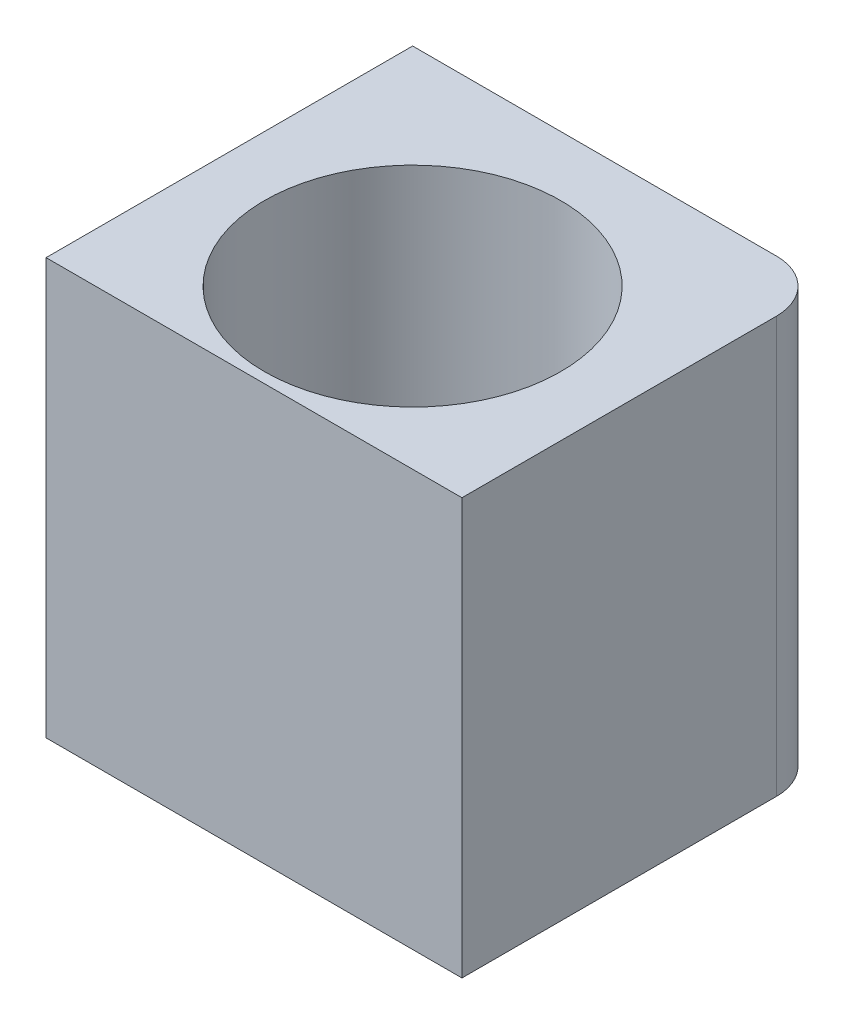
SolidWorks part; units mm, degrees
ref_plane "Alzado" through (0, 0, 0) normal (0, 0, 1) x (1, 0, 0)
ref_plane "Planta" through (0, 0, 0) normal (0, 1, 0) x (1, 0, 0)
ref_plane "Vista lateral" through (0, 0, 0) normal (1, 0, 0) x (0, 0, -1)
sketch "Croquis1" plane through (0, 0, 0) normal (0, 1, 0) x (1, 0, 0)
  line L0 (0, 20) -> (0, -20) construction
  line L1 (-20, 20) -> (20, 20)
  line L2 (-20, 20) -> (-20, -20)
  line L3 (-20, -20) -> (20, -20)
  line L4 (20, 20) -> (20, -20)
  line L5 (-20, 20) -> (20, -20) construction
  line L6 (-20, -20) -> (20, 20) construction
  line L7 (-20, -4.25) -> (-30, -7.25)
  line L8 (-30, -7.25) -> (-30, -15.25)
  line L9 (-30, -15.25) -> (30, -15.25)
  line L10 (20, -4.25) -> (30, -7.25)
  line L11 (30, -7.25) -> (30, -15.25)
  circle A0 centre (-15, 15) radius 2.125
  circle A1 centre (15, 15) radius 2.125
  circle A4 centre (0, 0) radius 15.25
  circle A5 centre (-15, -15) radius 2.125 [skipped]
  circle A6 centre (15, -15) radius 2.125 [skipped]
  point P0 (0, 0)
  point P25 (0, -15.25)
  dimension "D3" = 4.25
  dimension "D7" = 30.5
  dimension "D1" = 40
  dimension "D2" = 40
  dimension "D4" = 5
  dimension "D5" = 2
  dimension "D8" = 8
  dimension "D9" = 10
  dimension "D10" = 15.25
  dimension "D12" = 3
  dimension "D6" = 2
extrude "Soporte caja reductora" add sketch "Croquis1" against normal blind 20
sketch "Croquis3" plane through (0, 0, 15.25) normal (0, 0, 1) x (1, 0, 0)
  line L3 (-20, -20) -> (-20, 0) construction
  circle A0 centre (-23.5, -10) radius 2.125
  circle A1 centre (23.5, -10) radius 2.125
  dimension "D1" = 4.25
  dimension "D2" = 3.5
extrude "Cortar-Extruir1" cut sketch "Croquis3" against normal through all
fillet "Redondeo1" radius 5 2 edges at (-20, -10, -20) (20, -10, -20)
sketch "Sketch1" plane through (0, 0, 0) normal (0, 1, 0) x (1, 0, 0)
  line L0 (15, 20) -> (30, 20)
  line L1 (30, 20) -> (30, 8)
  line L2 (30, 8) -> (25.5, 8)
  line L4 (25.5, 8) -> (25.5, 15)
  line L5 (25.5, 15) -> (20, 15)
  circle A0 centre (15, 15) radius 5
  arc M37 (20, 15) -> (15, 20) centre (15, 15) ccw
  dimension "D1" = 12
  dimension "D2" = 5.5
extrude "Boss-Extrude1" add sketch "Sketch1" along direction (0, 1, 0) on the side against the normal up to surface (20 mm away) contours L5 L4 L2 L1 L0 M37
sketch "Sketch2" plane through (0, 0, -20) normal (0, 0, -1) x (-1, 0, 0)
  line L1 (-20, -20) -> (-20, 0) construction
  circle A0 centre (-22.75, -10) radius 1.625
  dimension "D1" = 3.25
  dimension "D2" = 2.75
extrude "Cut-Extrude1" cut sketch "Sketch2" against normal up to next
sketch "Sketch3" plane through (0, 0, -15) normal (0, 0, 1) x (1, 0, 0)
  line L1 (20, -11.5877) -> (22.75, -13.1754)
  line L2 (22.75, -13.1754) -> (25.5, -11.5877)
  line L3 (25.5, -11.5877) -> (25.5, -8.4123)
  line L4 (25.5, -8.4123) -> (22.75, -6.8246)
  line L5 (22.75, -6.8246) -> (20, -8.4123)
  line L6 (20, -8.4123) -> (20, -11.5877)
  circle A0 centre (22.75, -10) radius 2.75 construction
  dimension "D1" = 5.5
extrude "Cut-Extrude2" cut sketch "Sketch3" against normal blind 2
sketch "Sketch4" plane through (25.5, 0, 0) normal (-1, 0, 0) x (0, 0, 1)
  line L5 (-15, -8.4123) -> (-15, 0) construction
  line L6 (-20, 0) -> (-8, 0) construction
  circle A0 centre (-12.25, -10) radius 1.625
  dimension "D1" = 2.75
  dimension "D2" = 3.25
  dimension "D3" = 10
extrude "Cut-Extrude3" cut sketch "Sketch4" against normal through all
sketch "Sketch5" plane through (30, 0, 0) normal (1, 0, 0) x (0, 0, -1)
  line L1 (15, -11.5877) -> (15, -8.4123)
  line L2 (15, -8.4123) -> (12.25, -6.8246)
  line L3 (12.25, -6.8246) -> (9.5, -8.4123)
  line L4 (9.5, -8.4123) -> (9.5, -11.5877)
  line L5 (9.5, -11.5877) -> (12.25, -13.1754)
  line L6 (12.25, -13.1754) -> (15, -11.5877)
  circle A0 centre (12.25, -10) radius 2.75 construction
  dimension "D1" = 5.5
extrude "Cut-Extrude4" cut sketch "Sketch5" along normal blind 2 from surface
sketch "Croquis6" plane through (0, 0, 0) normal (0, 1, 0) x (1, 0, 0)
  line L0 (-20, -20) -> (20, -20) construction
  line L1 (-15.25, 0) -> (15.25, 0)
  line L2 (-15.25, 0) -> (-15.25, -20)
  line L3 (-15.25, -20) -> (15.25, -20)
  line L4 (15.25, 0) -> (15.25, -20)
  line L6 (-20, -20) -> (20, -20)
  line L7 (-20, -20) -> (-20, -15.25)
  line L8 (-20, -15.25) -> (20, -15.25)
  line L9 (20, -20) -> (20, -15.25)
  circle A0 centre (0, 0) radius 15.25 construction
  circle M5 centre (0, 0) radius 15.25
  line M14 (-20, -15.25) -> (-20, -20)
  line M15 (-20, -20) -> (20, -20)
  line M16 (20, -20) -> (20, -15.25)
extrude "Cortar-Extruir17" cut sketch "Croquis6" against normal through all contours L8 L2 L4 M15 | L8 L2 M14 M15 | L2 L8 M5 | L8 L4 M5 | L8 L4 M15 M16
mirror "Simetría1" about plane through (0, 0, 0) normal (0, 1, 0) of bodies 111
sketch "Croquis7" plane through (0, 0, -20) normal (0, 0, -1) x (-1, 0, 0)
  line L1 (-30, 0) -> (30, 0)
  line L2 (-30, 0) -> (-30, -20)
  line L3 (-30, -20) -> (30, -20)
  line L4 (30, 0) -> (30, -20)
extrude "Cortar-Extruir18" cut sketch "Croquis7" against normal through all
sketch "Croquis8" plane through (0, 20, 0) normal (0, 1, 0) x (1, 0, 0)
  line L3 (-15, 20) -> (30, 20) construction
  line L4 (-11.0405, 13.9391) -> (-10.3152, 11.2321)
  line L5 (10.8174, 13.8793) -> (10.3152, 11.2321)
  line L59 (10.8174, 13.8793) -> (11.9787, 20)
  line L60 (-11.0405, 13.9391) -> (-12.6645, 20)
  line L61 (11.9787, 20) -> (-12.6645, 20)
  circle A0 centre (0, 0) radius 15.25
extrude "Saliente-Extruir2" add sketch "Croquis8" along normal blind 49
sketch "Croquis9" plane through (0, 69, 0) normal (0, 1, 0) x (1, 0, 0)
  line L0 (-20, 0) -> (20, 0)
  line L1 (-20, 15) -> (-20, -4.25) construction
  line L2 (20, 15) -> (20, -4.25) construction
  line L3 (-20, 0) -> (-20, 15)
  line L4 (-15, 20) -> (12.6645, 20)
  line L5 (12.6645, 20) -> (20, 13.9368)
  line L6 (20, 13.9368) -> (20, 0)
  line L7 (20, 0) -> (20.1759, -0.147)
  line L8 (-14.75, 0) -> (-14.75, -15.25)
  line L9 (-15.25, -15.25) -> (-30, -15.25)
  line L10 (-30, -15.25) -> (-30, -7.25)
  line L11 (-30, -7.25) -> (-20, -4.25)
  line L12 (-20, -4.25) -> (-20, 0)
  line L13 (-14.75, -15.25) -> (-15.25, -15.25)
  line L14 (-14.75, -15.25) -> (0, -15.25)
  line L15 (0, -15.25) -> (0, -14.75)
  circle A0 centre (0, 0) radius 14.75
  circle A1 centre (-15, 15) radius 5
  dimension "D1" = 29.5
extrude "Soporte motor" add sketch "Croquis9" against normal blind 15 from offset 15 offset against normal yes
sketch "Croquis12" plane through (0, 0, 15.25) normal (0, 0, 1) x (1, 0, 0)
  line L1 (0, 54) -> (-30, 54) construction
  line L2 (-20, 39) -> (-20, 54) construction
  circle A0 centre (-23.5, 46.5) radius 2.125
  dimension "D3" = 4.25
  dimension "D1" = 7.5
  dimension "D2" = 3.5
extrude "Agujeros de sujecion a base" cut sketch "Croquis12" against normal through all
sketch "Croquis13" plane through (0, 0, 15.25) normal (0, 0, 1) x (1, 0, 0)
  line L1 (-20, 44.4793) -> (-20, 48.5207)
  line L2 (-20, 48.5207) -> (-23.5, 50.5415)
  line L3 (-23.5, 50.5415) -> (-27, 48.5207)
  line L4 (-27, 48.5207) -> (-27, 44.4793)
  line L5 (-27, 44.4793) -> (-23.5, 42.4585)
  line L6 (-23.5, 42.4585) -> (-20, 44.4793)
  circle A0 centre (-23.5, 46.5) radius 3.5 construction
  dimension "D1" = 7
extrude "Tuerca Agujero de sujecion a base" cut sketch "Croquis13" against normal blind 10 from offset 4 offset against normal yes
sketch "Croquis10" plane through (0, 69, 0) normal (0, 1, 0) x (1, 0, 0)
  line L0 (-10.3152, 11.2321) -> (-9.8079, 9.3388)
  line L1 (10.3152, 11.2321) -> (9.4813, 8.1201)
  circle A0 centre (0, 0) radius 14.75
  circle A1 centre (0, 0) radius 15.25
  arc M2 (-10.3152, 11.2321) -> (10.3152, 11.2321) centre (0, 0) cw
extrude "Saliente-Extruir4" add sketch "Croquis10" against normal up to surface (15 mm away) contours A0 L1 L0 M2
sketch "Croquis11" plane through (0, 0, 0) normal (0, -1, 0) x (1, 0, 0)
  line L0 (0, 0) -> (0, -12.6937) construction
  line L1 (15, -20) -> (30, -20)
  line L2 (30, -20) -> (30, 15.25)
  line L3 (30, 15.25) -> (15.25, 15.25)
  line L4 (15.25, 0) -> (15.25, 15.25) construction
  line L5 (15.25, 15.25) -> (30, 15.25) construction
  line L6 (15.25, 15.25) -> (15.25, 4.25)
  line L7 (15.25, 4.25) -> (20, 4.25)
  line L8 (20, 4.25) -> (20, -15)
  circle A0 centre (0, 0) radius 22.5
  circle A1 centre (-15, -15) radius 5
  circle A2 centre (15, -15) radius 5
  line M8 (-15, -20) -> (30, -20)
  line M9 (30, -20) -> (30, -8)
  line M10 (30, -8) -> (25.5, -8)
  line M11 (25.5, -8) -> (25.5, -15)
  line M12 (25.5, -15) -> (20, -15)
  line M14 (20, 4.25) -> (30, 7.25)
  line M15 (30, 7.25) -> (30, 15.25)
  line M16 (30, 15.25) -> (15.25, 15.25)
  line M17 (15.25, 15.25) -> (15.25, 0)
  dimension "D1" = 45
extrude "Cortar-Extruir19" cut sketch "Croquis11" against normal blind 25 contours A0 L3 L7 M14 M17 | A0 M14 M15 M16 | A2 M12 M8 M9 M10 M11
mirror "Simetría2"
sketch "Croquis14" plane through (0, 0, 15.25) normal (0, 0, 1) x (1, 0, 0)
  line L1 (-30, 20) -> (20, 20)
  line L2 (-30, 20) -> (-30, 138)
  line L3 (-30, 138) -> (20, 138)
  line L4 (20, 20) -> (20, 138)
extrude "Cortar-Extruir22" cut sketch "Croquis14" against normal through all
sketch "Croquis15" plane through (0, 0, 0) normal (0, -1, 0) x (1, 0, 0)
  line L0 (-30, 7.25) -> (-30, 15.25) construction
  line L1 (-20, 4.25) -> (-30, 4.25)
  line L2 (-20, 4.25) -> (-20, 11.25)
  line L3 (-20, 11.25) -> (-30, 11.25)
  line L4 (-30, 4.25) -> (-30, 11.25)
  line L5 (-30, 15.25) -> (-15.25, 15.25) construction
  dimension "D1" = 4
extrude "Cortar-Extruir23" cut sketch "Croquis15" against normal through all
sketch "Croquis16" plane through (0, 0, 0) normal (0, -1, 0) x (1, 0, 0)
  line L0 (-15.25, 0) -> (-15.25, 15.25) construction
  line L1 (-30, 15.25) -> (-15.25, 15.25)
  line L2 (-30, 15.25) -> (-30, 12.75)
  line L3 (-20, 12.75) -> (-15.25, 12.75)
  line L4 (-15.25, 15.25) -> (-15.25, 12.75)
  line L5 (-30, 12.75) -> (-30, 11.25)
  line L6 (-30, 11.25) -> (-20, 11.25)
  line L7 (-20, 11.25) -> (-30, 11.25) construction
  line L8 (-20, -15) -> (-20, 11.25) construction
  line L9 (-20, 11.25) -> (-20, 12.75)
  dimension "D1" = 2.5
extrude "Cortar-Extruir24" cut sketch "Croquis16" against normal through all
sketch "Croquis18" plane through (0, 0, -20) normal (0, 0, -1) x (-1, 0, 0)
  line L0 (20, 0) -> (20, 20) construction
  line L1 (-20, 0) -> (20, 0)
  line L2 (-20, 0) -> (-20, 10)
  line L3 (-20, 10) -> (20, 10)
  line L4 (20, 0) -> (20, 10)
  line L5 (15, 20) -> (-15, 20) construction
  dimension "D1" = 10
extrude "Cortar-Extruir25" cut sketch "Croquis18" against normal through all
sketch "Croquis19" plane through (0, 20, 0) normal (0, 1, 0) x (1, 0, 0)
  line L0 (-20, -12.75) -> (-34, -12.75)
  line L1 (-34, -12.75) -> (-34, -7.75)
  line L2 (-34, -7.75) -> (-24, -7.75)
  line L3 (-24, -7.75) -> (-20, -3.75)
  line L4 (-20, 15) -> (-20, -12.75) construction
  line L5 (-20, -3.75) -> (-20, -12.75)
  dimension "D1" = 5
  dimension "D2" = 4
  dimension "D3" = 4
  dimension "D4" = 10
extrude "Saliente-Extruir5" add sketch "Croquis19" against normal up to surface (10 mm away) up to face at (15, 10, -12.875)
sketch "Croquis20" plane through (0, 0, 7.75) normal (0, 0, -1) x (-1, 0, 0)
  circle A0 centre (29, 15) radius 1
  dimension "D1" = 2
extrude "Cortar-Extruir26" cut sketch "Croquis20" against normal through all
sketch "Croquis21" plane through (20, 0, 0) normal (1, 0, 0) x (0, 0, -1)
  line L1 (20, 20) -> (20, 10) construction
  circle A0 centre (4.75, 15) radius 1.625
  dimension "D1" = 3.25
  dimension "D2" = 15.25
extrude "Cortar-Extruir27" cut sketch "Croquis21" against normal up to next
sketch "Croquis22" plane through (0, 10, 0) normal (0, -1, 0) x (1, 0, 0)
  circle A0 centre (-15, -15) radius 2.125
  circle A1 centre (15, -15) radius 2.125
  circle A2 centre (15, -15) radius 1
  circle A3 centre (-15, -15) radius 1
  dimension "D1" = 2
extrude "Saliente-Extruir6" add sketch "Croquis22" against normal blind 10
sketch "Croquis23" plane through (0, 0, -20) normal (0, 0, -1) x (-1, 0, 0)
  circle A0 centre (0, 15) radius 1.625
  dimension "D1" = 3.25
extrude "Cortar-Extruir28" cut sketch "Croquis23" against normal through all
sketch "Croquis24" plane through (0, 0, -20) normal (0, 0, -1) x (-1, 0, 0)
  line L1 (1.5877, 12.25) -> (3.1754, 15)
  line L2 (3.1754, 15) -> (1.5877, 17.75)
  line L3 (1.5877, 17.75) -> (-1.5877, 17.75)
  line L4 (-1.5877, 17.75) -> (-3.1754, 15)
  line L5 (-3.1754, 15) -> (-1.5877, 12.25)
  line L6 (-1.5877, 12.25) -> (1.5877, 12.25)
  circle A0 centre (0, 15) radius 2.75 construction
  dimension "D1" = 5.5
extrude "Cortar-Extruir29" cut sketch "Croquis24" against normal blind 10 from offset 3 offset against normal yes
sketch "Croquis26" plane through (0, 10, 0) normal (0, -1, 0) x (1, 0, 0)
  line L0 (-29, 12.75) -> (-58.825, 12.75)
  line L1 (-58.825, 12.75) -> (-39.1605, -4.1045)
  line L3 (-39.5945, 1.5357) -> (-46.8449, 7.75)
  line L4 (-46.8449, 7.75) -> (-34.2682, 7.75)
  line L5 (-34.2682, 7.75) -> (-39.5945, 1.5357)
  line L7 (-29, 7.75) -> (-35.7321, -0.1045)
  line L8 (-29, 7.75) -> (-29, 12.75)
  line L9 (-34, 7.75) -> (-24, 7.75) construction
  line L10 (-34, 12.75) -> (-15.25, 12.75) construction
  line L11 (-39.1605, -4.1045) -> (-20, -4.1045)
  line L12 (-20, 3.75) -> (-20, -15) construction
  line L13 (-20, -4.1045) -> (-20, -0.1045)
  line L14 (-20, -0.1045) -> (-35.7321, -0.1045)
  dimension "D1" = 4
  dimension "D2" = 4
  dimension "D3" = 4
  dimension "D4" = 29.825
  dimension "D5" = 40.6
extrude "Saliente-Extruir7" add sketch "Croquis26" against normal blind 10
sketch "Croquis27" plane through (0, 0, 12.75) normal (0, 0, 1) x (1, 0, 0)
  line L0 (-29, 16) -> (-29, 14) construction
  line L1 (-46.8449, 20) -> (-46.8449, 10) construction
  circle A0 centre (-40.5449, 15) radius 1.625
  circle A2 centre (-29, 15) radius 1.625
  dimension "D1" = 3.25
  dimension "D2" = 6.3
extrude "Cortar-Extruir30" cut sketch "Croquis27" against normal up to next
sketch "Croquis28" plane through (0, 0, 12.75) normal (0, 0, 1) x (1, 0, 0)
  line L1 (-38.9572, 12.25) -> (-37.3694, 15)
  line L2 (-37.3694, 15) -> (-38.9572, 17.75)
  line L3 (-38.9572, 17.75) -> (-42.1326, 17.75)
  line L4 (-42.1326, 17.75) -> (-43.7203, 15)
  line L5 (-43.7203, 15) -> (-42.1326, 12.25)
  line L6 (-42.1326, 12.25) -> (-38.9572, 12.25)
  line L7 (-27.4123, 12.25) -> (-25.8246, 15)
  line L8 (-25.8246, 15) -> (-27.4123, 17.75)
  line L9 (-27.4123, 17.75) -> (-30.5877, 17.75)
  line L10 (-30.5877, 17.75) -> (-32.1754, 15)
  line L11 (-32.1754, 15) -> (-30.5877, 12.25)
  line L12 (-30.5877, 12.25) -> (-27.4123, 12.25)
  circle A0 centre (-40.5449, 15) radius 2.75 construction
  circle A1 centre (-29, 15) radius 2.75 construction
  dimension "D1" = 5.5
extrude "Cortar-Extruir31" cut sketch "Croquis28" against normal up to next from offset 3 offset against normal yes
sketch "Croquis29" plane through (-18.6128, 0, -21.716) normal (-0.6508, 0, -0.7593) x (-0.7593, 0, 0.6508)
  line L2 (31.0624, 20) -> (31.0624, 10) construction
  circle A0 centre (33.8124, 15) radius 1.625
  dimension "D2" = 3.25
  dimension "D1" = 2.75
extrude "Cortar-Extruir32" cut sketch "Croquis29" against normal up to next
sketch "Croquis31" plane through (-18.6128, 0, -21.716) normal (-0.6508, 0, -0.7593) x (-0.7593, 0, 0.6508)
  line L1 (36.5624, 16.5877) -> (33.8124, 18.1754)
  line L2 (33.8124, 18.1754) -> (31.0624, 16.5877)
  line L3 (31.0624, 16.5877) -> (31.0624, 13.4123)
  line L4 (31.0624, 13.4123) -> (33.8124, 11.8246)
  line L5 (33.8124, 11.8246) -> (36.5624, 13.4123)
  line L6 (36.5624, 13.4123) -> (36.5624, 16.5877)
  circle A0 centre (33.8124, 15) radius 2.75 construction
  dimension "D1" = 5.5
extrude "Cortar-Extruir33" cut sketch "Croquis31" against normal up to next from offset 2.5 offset against normal yes
sketch "Croquis35" plane through (0, 20, 0) normal (0, 1, 0) x (1, 0, 0)
  line L0 (-15, 20) -> (15, 20) construction
  line L1 (10.3896, 0) -> (23.695, 0)
  line L2 (10.3896, 0) -> (10.3896, -6.8269)
  line L3 (10.3896, -6.8269) -> (23.695, -6.8269)
  line L4 (23.695, 0) -> (23.695, -6.8269)
  dimension "D1" = 20
extrude "Cortar-Extruir34" cut sketch "Croquis35" against normal through all both and the other way through all
sketch "Croquis36" plane through (20, 0, 0) normal (1, 0, 0) x (0, 0, -1)
  line L1 (7.5, 16.5877) -> (4.75, 18.1754)
  line L2 (4.75, 18.1754) -> (2, 16.5877)
  line L3 (2, 16.5877) -> (2, 13.4123)
  line L4 (2, 13.4123) -> (4.75, 11.8246)
  line L5 (4.75, 11.8246) -> (7.5, 13.4123)
  line L6 (7.5, 13.4123) -> (7.5, 16.5877)
  circle A0 centre (4.75, 15) radius 2.75 construction
  dimension "D1" = 5.5
extrude "Cortar-Extruir35" cut sketch "Croquis36" against normal blind 10 from offset 3 offset against normal yes
sketch "Croquis37" plane through (0, 10, 0) normal (0, -1, 0) x (1, 0, 0)
  line L0 (-39.1605, -4.1045) -> (-20.6149, -20)
  line L1 (-20.6149, -20) -> (-15, -20)
  line L2 (-33.014, -4.1045) -> (-19.5581, -15.6376)
  line L3 (-39.1605, -4.1045) -> (-20, -4.1045) construction
  line L4 (-19.5581, -15.6376) -> (-15, -20)
  line L5 (-58.825, 12.75) -> (-39.1605, -4.1045) construction
  line L6 (-39.5945, 1.5357) -> (-46.8449, 7.75) construction
  line L7 (-39.1605, -4.1045) -> (-33.014, -4.1045)
extrude "Saliente-Extruir8" add sketch "Croquis37" against normal blind 10
sketch "Croquis38" plane through (0, 10, 0) normal (0, -1, 0) x (1, 0, 0)
  line L0 (-58.825, 12.75) -> (-38.825, 12.75)
  line L1 (-58.825, 12.75) -> (-15.25, 12.75) construction
  line L2 (-38.825, 12.75) -> (-38.825, 9.75)
  line L3 (-38.825, 9.75) -> (-55.3248, 9.75)
  line L4 (-58.825, 12.75) -> (-20.6149, -20) construction
  line L5 (-55.3248, 9.75) -> (-58.825, 12.75)
  dimension "D1" = 3
  dimension "D2" = 20
extrude "Saliente-Extruir9" add sketch "Croquis38" along normal blind 13
sketch "Croquis39" plane through (0, 10, 0) normal (0, -1, 0) x (1, 0, 0)
  line L0 (-38.825, 9.75) -> (-38.825, 7.75)
  line L1 (-46.8449, 7.75) -> (-34.2682, 7.75) construction
  line L3 (-55.3248, 9.75) -> (-20.6149, -20) construction
  line L4 (-52.9914, 7.75) -> (-55.3248, 9.75)
  line L5 (-55.3248, 9.75) -> (-38.825, 9.75)
  line L6 (-52.9914, 7.75) -> (-50.658, 5.75)
  line L7 (-50.658, 5.75) -> (-38.825, 5.75)
  line L8 (-38.825, 5.75) -> (-38.825, 7.75)
  dimension "D1" = 2
extrude "Saliente-Extruir10" add sketch "Croquis39" along normal blind 3
mirror "Simetría3" of bodies 142
sketch "Croquis40" plane through (0, 0, -20) normal (0, 0, -1) x (-1, 0, 0)
  line L1 (-30.8963, 20) -> (75.6873, 20)
  line L2 (-30.8963, 20) -> (-30.8963, -27.3915)
  line L3 (-30.8963, -27.3915) -> (75.6873, -27.3915)
  line L4 (75.6873, 20) -> (75.6873, -27.3915)
extrude "Cortar-Extruir36" cut sketch "Croquis40" against normal through all both and the other way through all
sketch "Croquis41" plane through (0, 20, 0) normal (0, -1, 0) x (1, 0, 0)
  line L0 (-19.993, -22.3025) -> (-20, 3.75)
  line L1 (-20, 3.75) -> (-24, 7.75)
  line L2 (-24, 7.75) -> (-56.0351, 7.75)
  line L3 (-56.0351, 7.75) -> (-19.993, -22.3025)
extrude "Cortar-Extruir37" cut sketch "Croquis41" against normal through all both and the other way through all
sketch "Croquis42" plane through (0, 0, 9.75) normal (0, 0, -1) x (-1, 0, 0)
  line L0 (46.7203, 20) -> (46.7203, 30)
  line L1 (52.9914, 20) -> (24, 20) construction
  line L2 (46.7203, 30) -> (38.825, 30)
  line L3 (38.825, 30) -> (33.493, 43.7606)
  line L4 (33.493, 43.7606) -> (49.5253, 48.9514)
  line L5 (49.5253, 48.9514) -> (67.2004, 42.5122)
  line L6 (67.2004, 42.5122) -> (65.9066, 20)
  line L7 (65.9066, 20) -> (51.714, 13.8642)
  line L8 (51.714, 13.8642) -> (46.7203, 20)
  dimension "D1" = 3
extrude "Cortar-Extruir38" cut sketch "Croquis42" against normal through all both and the other way through all
sketch "Croquis43" plane through (0, 20, 0) normal (0, -1, 0) x (1, 0, 0)
  line L0 (-19.9936, -20) -> (-46.7203, 7.75)
  line L1 (-19.9936, -20) -> (-17.1126, -17.2252)
  line L2 (-46.7203, 7.75) -> (-43.8393, 10.5248)
  line L3 (-17.1126, -17.2252) -> (-43.8393, 10.5248)
  dimension "D1" = 4
extrude "Saliente-Extruir11" add sketch "Croquis43" against normal up to vertex (10 mm away)
sketch "Croquis44" plane through (0, 0, 9.75) normal (0, 0, -1) x (-1, 0, 0)
  line L7 (38.9572, 27.75) -> (37.3694, 25)
  line L8 (37.3694, 25) -> (38.9572, 22.25)
  line L9 (38.9572, 22.25) -> (42.1326, 22.25)
  line L10 (42.1326, 22.25) -> (43.7203, 25)
  line L11 (43.7203, 25) -> (42.1326, 27.75)
  line L12 (42.1326, 27.75) -> (38.9572, 27.75)
  circle A1 centre (40.5449, 25) radius 2.75 construction
extrude "Cortar-Extruir39" cut sketch "Croquis44" along normal through all
sketch "Croquis45" plane through (0, 0, 12.75) normal (0, 0, 1) x (1, 0, 0)
  line L1 (-46.7203, 30) -> (-15.25, 30)
  line L2 (-46.7203, 30) -> (-46.7203, 20)
  line L3 (-46.7203, 20) -> (-15.25, 20)
  line L4 (-15.25, 30) -> (-15.25, 20)
  circle A0 centre (-40.5449, 25) radius 1.625
  circle A1 centre (-29, 25) radius 1.625
extrude "Saliente-Extruir12" add sketch "Croquis45" along normal blind 2.5
sketch "Croquis46" plane through (0, 20, 0) normal (0, -1, 0) x (1, 0, 0)
  line L0 (15.25, 0) -> (20, 0)
  line L1 (20, 0) -> (20, 15.25)
  line L2 (-46.7203, 15.25) -> (-15.25, 15.25) construction
  line L3 (20, 15.25) -> (7.5498, 15.25)
  line L4 (7.5498, 15.25) -> (7.5498, 13.25)
  line L5 (-15.25, 0) -> (-15.25, 15.25)
  line L6 (-15.25, 15.25) -> (-7.5498, 15.25)
  line L7 (-7.5498, 15.25) -> (-7.5498, 13.25)
  arc A0 (-7.5498, 13.25) -> (-15.25, 0) centre (0, 0) ccw
  arc A1 (15.25, 0) -> (7.5498, 13.25) centre (0, 0) ccw
  dimension "D1" = 2
extrude "Saliente-Extruir13" add sketch "Croquis46" against normal up to vertex (10 mm away)
sketch "Croquis47" plane through (0, 0, 15.25) normal (0, 0, 1) x (1, 0, 0)
  line L1 (15.4123, 22.3525) -> (17, 25.1025)
  line L2 (17, 25.1025) -> (15.4123, 27.8525)
  line L3 (15.4123, 27.8525) -> (12.2369, 27.8525)
  line L4 (12.2369, 27.8525) -> (10.6491, 25.1025)
  line L5 (10.6491, 25.1025) -> (12.2369, 22.3525)
  line L6 (12.2369, 22.3525) -> (15.4123, 22.3525)
  line L10 (20, 30) -> (20, 20) construction
  line L11 (0, 20) -> (0, 0) construction
  line L12 (-15.25, 20) -> (15.25, 20) construction
  line L13 (-12.2369, 22.3525) -> (-15.4123, 22.3525)
  line L14 (-10.6491, 25.1025) -> (-12.2369, 22.3525)
  line L15 (-12.2369, 27.8525) -> (-10.6491, 25.1025)
  line L16 (-15.4123, 27.8525) -> (-12.2369, 27.8525)
  line L17 (-17, 25.1025) -> (-15.4123, 27.8525)
  line L18 (-15.4123, 22.3525) -> (-17, 25.1025)
  circle A0 centre (13.8246, 25.1025) radius 2.75 construction
  circle A1 centre (13.8246, 25.1025) radius 1.625
  circle A2 centre (-13.8246, 25.1025) radius 2.75 construction
  circle A3 centre (-13.8246, 25.1025) radius 1.625
  dimension "D1" = 3.25
  dimension "D2" = 5.5
  dimension "D3" = 3
extrude "Cortar-Extruir40" cut sketch "Croquis47" against normal blind 10 from offset 2 offset against normal yes
sketch "Croquis48" plane through (0, 0, 15.25) normal (0, 0, 1) x (1, 0, 0)
  circle A0 centre (13.8246, 25.1025) radius 1.625
  circle A1 centre (-13.8246, 25.1025) radius 1.625
extrude "Cortar-Extruir41" cut sketch "Croquis48" against normal up to vertex
sketch "Croquis49" plane through (0, 20, 0) normal (0, -1, 0) x (1, 0, 0)
  line L1 (-19.9936, -20) -> (-54.7897, -20)
  line L2 (-19.9936, -20) -> (-19.9936, 22.211)
  line L3 (-19.9936, 22.211) -> (-54.7897, 22.211)
  line L4 (-54.7897, -20) -> (-54.7897, 22.211)
extrude "Cortar-Extruir42" cut sketch "Croquis49" against normal through all both and the other way through all
sketch "Croquis51" plane through (0, 30, 0) normal (0, 1, 0) x (1, 0, 0)
  circle A0 centre (0, 0) radius 15.25
  circle A1 centre (0, 0) radius 14.25
  dimension "D1" = 28.5
extrude "Saliente-Extruir14" add sketch "Croquis51" against normal blind 10
sketch "Croquis52" plane through (0, 0, 13.25) normal (0, 0, -1) x (-1, 0, 0)
  line L1 (-10.6491, 25.1025) -> (-12.2369, 27.8525)
  line L2 (-12.2369, 27.8525) -> (-15.4123, 27.8525)
  line L3 (-15.4123, 27.8525) -> (-17, 25.1025)
  line L4 (-17, 25.1025) -> (-15.4123, 22.3525)
  line L5 (-15.4123, 22.3525) -> (-12.2369, 22.3525)
  line L6 (-12.2369, 22.3525) -> (-10.6491, 25.1025)
  line L7 (17, 25.1025) -> (15.4123, 27.8525)
  line L8 (15.4123, 27.8525) -> (12.2369, 27.8525)
  line L9 (12.2369, 27.8525) -> (10.6491, 25.1025)
  line L10 (10.6491, 25.1025) -> (12.2369, 22.3525)
  line L11 (12.2369, 22.3525) -> (15.4123, 22.3525)
  line L12 (15.4123, 22.3525) -> (17, 25.1025)
  circle A0 centre (-13.8246, 25.1025) radius 2.75 construction
  circle A1 centre (13.8246, 25.1025) radius 2.75 construction
extrude "Cortar-Extruir43" cut sketch "Croquis52" along normal blind 10
sketch "Croquis53" plane through (0, 0, -17) normal (0, 0, 1) x (1, 0, 0)
  line L1 (3.1754, 25) -> (1.5877, 27.75)
  line L2 (1.5877, 27.75) -> (-1.5877, 27.75)
  line L3 (-1.5877, 27.75) -> (-3.1754, 25)
  line L4 (-3.1754, 25) -> (-1.5877, 22.25)
  line L5 (-1.5877, 22.25) -> (1.5877, 22.25)
  line L6 (1.5877, 22.25) -> (3.1754, 25)
  circle A0 centre (0, 25) radius 2.75 construction
extrude "Cortar-Extruir44" cut sketch "Croquis53" along normal blind 10
sketch "Croquis54" plane through (17, 0, 0) normal (-1, 0, 0) x (0, 0, 1)
  line L1 (-4.75, 28.1754) -> (-7.5, 26.5877)
  line L2 (-7.5, 26.5877) -> (-7.5, 23.4123)
  line L3 (-7.5, 23.4123) -> (-4.75, 21.8246)
  line L4 (-4.75, 21.8246) -> (-2, 23.4123)
  line L5 (-2, 23.4123) -> (-2, 26.5877)
  line L6 (-2, 26.5877) -> (-4.75, 28.1754)
  circle A0 centre (-4.75, 25) radius 2.75 construction
extrude "Cortar-Extruir45" cut sketch "Croquis54" along normal blind 10
sketch "Croquis55" plane through (0, 30, 0) normal (0, 1, 0) x (1, 0, 0)
  line L0 (-7.5498, -15.25) -> (7.5498, -15.25)
  line L1 (7.5498, -15.25) -> (7.5498, -13.25)
  line L2 (-7.5498, -15.25) -> (-7.5498, -13.25)
  arc A0 (-7.5498, -13.25) -> (7.5498, -13.25) centre (0, 0) ccw
  line M5 (-7.5498, -15.25) -> (-7.5498, -13.25)
  arc M6 (-7.5498, -13.25) -> (7.5498, -13.25) centre (0, 0) ccw
  line M7 (7.5498, -13.25) -> (7.5498, -15.25)
extrude "Saliente-Extruir15" add sketch "Croquis55" against normal blind 10 contours L0 M5 M6 | L0 M6 M7
sketch "Croquis56" plane through (0, 30, 0) normal (0, 1, 0) x (1, 0, 0)
  line L24 (20, -15.25) -> (20, 15)
  line L25 (15, 20) -> (-19.9936, 20)
  line L26 (-19.9936, 20) -> (-19.9936, -15.25)
  line L27 (-19.9936, -15.25) -> (20, -15.25)
  line L28 (20, -15.25) -> (20, 15)
  line L29 (15, 20) -> (-19.9936, 20)
  line L30 (-19.9936, 20) -> (-19.9936, -15.25)
  line L31 (-19.9936, -15.25) -> (20, -15.25)
  circle A9 centre (0, 0) radius 14.25
  arc A10 (20, 15) -> (15, 20) centre (15, 15) ccw
  arc A11 (20, 15) -> (15, 20) centre (15, 15) ccw
  dimension "D1" = 0
extrude "Saliente-Extruir16" add sketch "Croquis56" along normal blind 40
sketch "Croquis57" plane through (-19.9936, 0, 0) normal (-1, 0, 0) x (0, 0, 1)
  line L0 (-20, 20) -> (-20, 70) construction
  line L1 (15.25, 20) -> (-20, 20)
  line L2 (15.25, 20) -> (15.25, 30)
  line L3 (15.25, 30) -> (-20, 30)
  line L4 (-20, 20) -> (-20, 30)
  line L5 (-20, 70) -> (15.25, 70) construction
  dimension "D1" = 40
extrude "Cortar-Extruir46" cut sketch "Croquis57" against normal through all both and the other way through all
